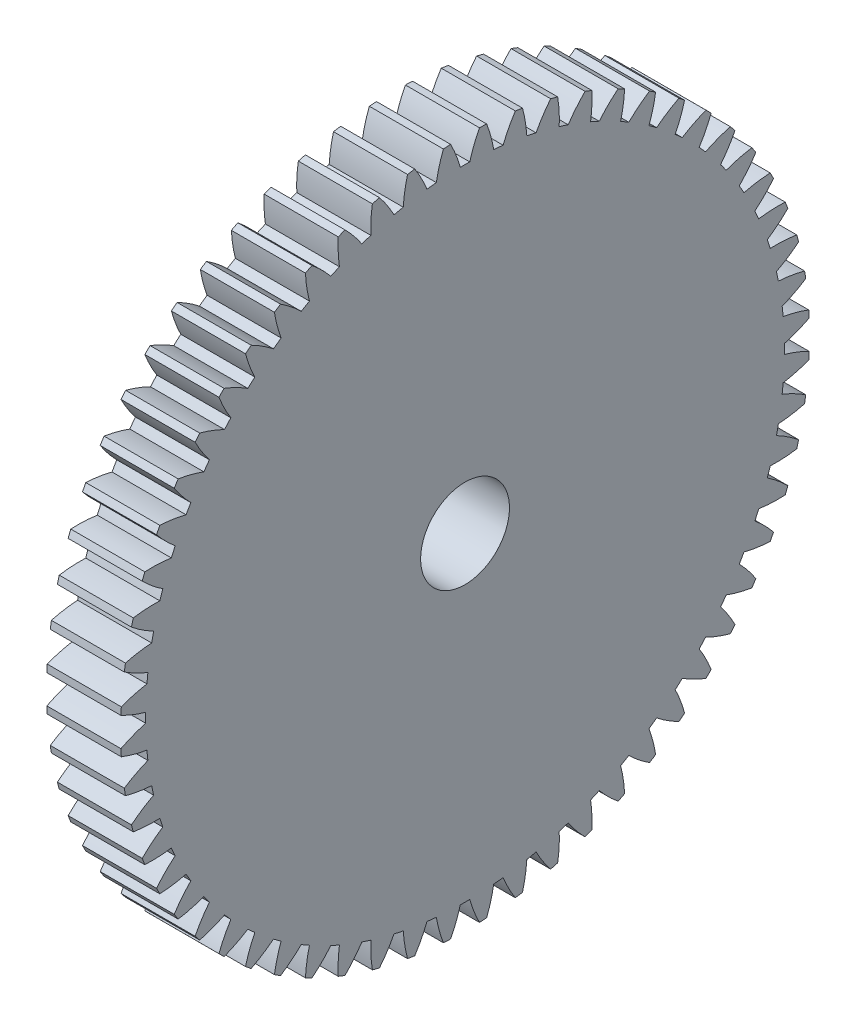
SolidWorks part; units mm, degrees
ref_plane "Plane1" through (0, 0, 0) normal (0, 0, 1) x (1, 0, 0)
ref_plane "Plane2" through (0, 0, 0) normal (0, 1, 0) x (1, 0, 0)
ref_plane "Plane3" through (0, 0, 0) normal (1, 0, 0) x (0, 0, -1)
other "Configuration Table"
sketch "HoldingSke" plane through (0, 0, 0) normal (0, 1, 0) x (1, 0, 0)
  line L0 (0, 0) -> (0.3333, -0.5774)
  line L1 (-15, 0) -> (100, 0) construction
  line L2 (0, 0) -> (-2.1039, 2.3779)
  line L3 (0, 0) -> (-11.863, 4.5341)
  line L4 (0, 0) -> (4.318, 7.479)
  line L5 (0, 0) -> (-46.8476, -17.4728)
  line L6 (0, 0) -> (-8.2896, -5.593)
  line L7 (-2.1039, 2.3779) -> (8.6586, 51.2059)
  line L8 (-76.2, 54.61) -> (-73.9, 54.61)
  line L9 (-71.009, 38.7566) -> (-53.1078, 45.2721)
  line L10 (-76.2, 71.12) -> (104.1128, 71.12)
  line L11 (0, 0) -> (-10, 0)
  line L12 (-76.2, 101.6) -> (-76.147, 101.6)
  line L13 (24.9733, 27.94) -> (52.9518, 28.4284)
  line L14 (24.9733, 27.94) -> (24.9743, 27.94)
  line L15 (24.9733, 27.94) -> (100.4006, 29.5858)
  line L16 (-63.627, -1.5) -> (-12.827, -1.5)
  circle A0 centre (0, 0) radius 6
  circle A1 centre (0, 0) radius 37.5
  circle A2 centre (0, 0) radius 37.5
  circle A3 centre (0, 0) radius 6
  dimension "MHD" = 75
  dimension "Hub_dia" = 75
  dimension "Bore" = 12
  dimension "MBD" = 12
  dimension "Num_teeth" = 60
  dimension "Pitch" = 0.6667
  dimension "Overall_len" = 50
  dimension "Show_teeth" = 60
  dimension "Thickness" = 10
  dimension "OAL" = 50.0001
  dimension "T_dim" = 2.3
  dimension "Ap" = 20
  dimension "H" = 19.05
  dimension "Pitch_radius" = 180.3128
  dimension "Width" = 10
  dimension "Backlash" = 0.053
  dimension "Addendum_fac" = 1
  dimension "Dedendum_fac" = 1.25
  dimension "Clearance_fac" = 0.25
  dimension "Dedendum_add" = 0.001
  dimension "Module" = 1.5
sketch "BasProSke" plane through (0, 0, 0) normal (0, 1, 0) x (1, 0, 0)
  line L0 (-10, 0) -> (60, 0) construction
  line L1 (0, 0) -> (0, 46.5)
  line L2 (0, 0) -> (10, 0)
  line L3 (10, 0) -> (10, 46.5)
  line L4 (10, 46.5) -> (0, 46.5)
  dimension "Thickness" = 10
  dimension "Diameter" = 93
revolve "Base-Revolve" add sketch "BasProSke" angle 360 about L0
sketch "TooCutSke" plane through (0, 0, 0) normal (1, 0, 0) x (0, 0, -1)
  line L1 (0, 0) -> (0, 107) construction
  line L2 (0, 0) -> (-1.2707, 44.9821) construction
  line L3 (0, 0) -> (-4.7089, 89.8505) construction
  line L4 (-1.2707, 44.9821) -> (-2.3544, 44.9253) construction
  arc A0 (0.6387, 43.1193) -> (-0.6387, 43.1193) centre (0, 0) ccw
  arc A1 (1.9554, 46.4843) -> (-1.9554, 46.4843) centre (0, 0) ccw
  circle A2 centre (0, 0) radius 45 construction
  circle A3 centre (0, 0) radius 42.2862 construction
  arc A4 (-0.6387, 43.1193) -> (-1.9554, 46.4843) centre (-17.9747, 38.2757) ccw
  arc A5 (1.9554, 46.4843) -> (0.6387, 43.1193) centre (17.9747, 38.2757) ccw
  dimension "Root_dia" = 86.248
  dimension "Overcut_dia" = 93.0508
  dimension "Pitch_dia" = 90
  dimension "Base_dia" = 84.5723
  dimension "Flank_rad" = 18
  dimension "Half_ang" = 3
  dimension "Half_CT" = 1.0852
extrude "ToothCut" cut sketch "TooCutSke" along normal through all
fillet "Breaks" [suppressed] radius 0.03
fillet "RootFillets" [suppressed] radius 0.376
pattern_circular "TeethCuts" count 60 every 6 about axis through (-10, 0, 0) along (1, 0, 0) of "ToothCut", "RootFillets", "Breaks"
sketch "HubNeaOneSke" plane through (0, 0, 0) normal (-1, 0, 0) x (0, 0, 1)
  circle A0 centre (0, 0) radius 37.5
  dimension "Diameter" = 75
extrude "HubNearOne" [suppressed] add sketch "HubNeaOneSke" along normal blind 40.0001
sketch "HubNeaBotSke" plane through (0, 0, 0) normal (-1, 0, 0) x (0, 0, 1)
  circle A0 centre (0, 0) radius 37.5
  dimension "Diameter" = 75
extrude "HubNearBoth" [suppressed] add sketch "HubNeaBotSke" along normal blind 20
ref_plane "FarPln" through (10, 0, 0) normal (1, 0, 0) x (0, 0, -1)
sketch "HubFarSke" plane through (10, 0, 0) normal (1, 0, 0) x (0, 0, -1)
  circle A0 centre (0, 0) radius 37.5
  dimension "Diameter" = 75
extrude "HubFar" [suppressed] add sketch "HubFarSke" along normal blind 20
sketch "BorSke" plane through (0, 0, 0) normal (1, 0, 0) x (0, 0, -1)
  circle A0 centre (0, 0) radius 6
  dimension "Diameter" = 12
extrude "Bore" cut sketch "BorSke" along normal mid plane 100.0001
sketch "KeySke" plane through (0, 0, 0) normal (1, 0, 0) x (0, 0, -1)
  line L0 (-2.5, 0) -> (-2.5, 8.3)
  line L1 (-2.5, 8.3) -> (2.5, 8.3)
  line L2 (2.5, 8.3) -> (2.5, 0)
  line L3 (0, 0) -> (0, 34) construction
  line L4 (-2.5, 0) -> (2.5, 0)
  dimension "Offset" = 8.3
  dimension "Width" = 5
extrude "Keyway" [suppressed] cut sketch "KeySke" along normal mid plane 100.0001
pattern_circular "Keyway2" [suppressed] count 2 every 90 about axis through (-10, 0, 0) along (1, 0, 0)
equation "' \"Module@HoldingSke\" = 6.35"
equation "' \"Num_teeth@HoldingSke\" = 12"
equation "' \"Ap@HoldingSke\" =  20"
equation "' \"Ap@HoldingSke\" = 20"
equation "' \"Width@HoldingSke\" = 0.5 * 25.4"
equation "' \"Hub_dia@HoldingSke\"= 1 * 25.4"
equation "' \"Hub_dia@HoldingSke\" = 1 * 25.4"
equation "' \"Overall_len@HoldingSke\" = 1.0 * 25.4"
equation "' \"Bore@HoldingSke\" = 0.75 * 25.4"
equation "' \"T_dim@HoldingSke\" = 0.1 * 25.4"
equation "' \"Width@KeySke\" = 0.25 * 25.4"
equation "' \"Show_teeth@HoldingSke\" = 13"
equation "' \"Backlash@HoldingSke\" = 0.009 * 25.4"
equation "' \"Addendum_fac@HoldingSke\" = 1.0"
equation "' \"Dedendum_fac@HoldingSke\" = 1.25"
equation "' \"Dedendum_add@HoldingSke\" = 0.00005 * 25.4"
equation "' \"Clearance_fac@HoldingSke\" = 0.25"
equation "\"Pitch@HoldingSke\" = 1 / \"Module@HoldingSke\""
equation "\"Overcut_dia@TooCutSke\" = (\"Num_teeth@HoldingSke\" + 2 * \"Addendum_fac@HoldingSke\") / \"Pitch@HoldingSke\" + 0.002 * 25.4"
equation "\"Pitch_dia@TooCutSke\" = \"Num_teeth@HoldingSke\" / \"Pitch@HoldingSke\""
equation "\"Base_dia@TooCutSke\" = \"Num_teeth@HoldingSke\" / \"Pitch@HoldingSke\" * cos((\"Ap@HoldingSke\"  * 3.14159265 / 180))"
equation "\"Root_dia@TooCutSke\" = (\"Num_teeth@HoldingSke\" + 2) / \"Pitch@HoldingSke\" - 2 * (\"Addendum_fac@HoldingSke\" + \"Dedendum_fac@HoldingSke\") / \"Pitch@HoldingSke\" - \"Dedendum_add@HoldingSke\" * 2"
equation "\"Half_ang@TooCutSke\" = 180 / \"Num_teeth@HoldingSke\""
equation "\"Half_CT@TooCutSke\" = \"Num_teeth@HoldingSke\" / \"Pitch@HoldingSke\" * sin((3.14159265 / 2 / \"Num_teeth@HoldingSke\")) / 2 - 7 * \"Backlash@HoldingSke\" / 4"
equation "\"Flank_rad@TooCutSke\" = \"Num_teeth@HoldingSke\" / \"Pitch@HoldingSke\" / 5"
equation "\"Radius@RootFillets\" = \"Clearance_fac@HoldingSke\" / \"Pitch@HoldingSke\" + \"Dedendum_add@HoldingSke\""
equation "\"Break_rad@Breaks\" = 0.02 / \"Pitch@HoldingSke\""
equation "\"Thickness@HoldingSke\" = \"Width@HoldingSke\""
equation "\"OAL@HoldingSke\" = \"Thickness@HoldingSke\""
equation "\"MHD@HoldingSke\" = (\"Num_teeth@HoldingSke\" + 2) / \"Pitch@HoldingSke\" - 2 * (\"Addendum_fac@HoldingSke\" + \"Dedendum_fac@HoldingSke\")  / \"Pitch@HoldingSke\" - \"Dedendum_add@HoldingSke\" * 2"
equation "\"MBD@HoldingSke\" = (\"Num_teeth@HoldingSke\" + 2) / \"Pitch@HoldingSke\" - 2 * (\"Addendum_fac@HoldingSke\" + \"Dedendum_fac@HoldingSke\")  / \"Pitch@HoldingSke\" - \"Dedendum_add@HoldingSke\" * 2 - 0.002 * 25.4"
equation "\"MHD@HoldingSke\" = ((sgn( \"MHD@HoldingSke\" - \"Hub_dia@HoldingSke\" )-1)*( \"MHD@HoldingSke\" - \"Hub_dia@HoldingSke\" ))/-2+ \"Hub_dia@HoldingSke\""
equation "\"MBD@HoldingSke\" = ((sgn( \"MBD@HoldingSke\" - \"Bore@HoldingSke\" )-1)*( \"MBD@HoldingSke\" - \"Bore@HoldingSke\" ))/-2+ \"Bore@HoldingSke\""
equation "\"OAL@HoldingSke\" = ((sgn( \"OAL@HoldingSke\" - \"Overall_len@HoldingSke\" )+1)*( \"OAL@HoldingSke\" - \"Overall_len@HoldingSke\" ))/2 + \"Overall_len@HoldingSke\" + 0.000002 * 25.4"
equation "\"Num_teeth@TeethCuts\" = int( \"Show_teeth@HoldingSke\" ) + 1"
equation "\"Num_teeth@TeethCuts\" = ((sgn( \"Num_teeth@TeethCuts\" - \"Num_teeth@HoldingSke\" )-1)*( \"Num_teeth@TeethCuts\" - \"Num_teeth@HoldingSke\" ))/-2+ \"Num_teeth@HoldingSke\""
equation "\"Num_teeth@TeethCuts\" = ((sgn( \"Num_teeth@TeethCuts\" - 2.0)+1)*( \"Num_teeth@TeethCuts\" - 2.0))/2 +2.0"
equation "\"Angle@TeethCuts\" = 360.0 / \"Num_teeth@HoldingSke\""
equation "\"Diameter@BasProSke\" = (\"Num_teeth@HoldingSke\" + 2 * \"Addendum_fac@HoldingSke\") / \"Pitch@HoldingSke\""
equation "\"Thickness@BasProSke\"  = \"Thickness@HoldingSke\""
equation "' \"Fillet_rad@BasProSke\" =  \"Thickness@HoldingSke\" * 0.05"
equation "' \"Fillet_rad@BasProSke\" = \"Thickness@HoldingSke\" * 0.05"
equation "\"MHD@HoldingSke\" = ((sgn( \"MHD@HoldingSke\" - \"Root_dia@TooCutSke\" )-1)*( \"MHD@HoldingSke\" - \"Root_dia@TooCutSke\" ))/-2+ \"Root_dia@TooCutSke\""
equation "\"Diameter@HubNeaOneSke\" = \"MHD@HoldingSke\""
equation "\"Length@HubNearOne\" = \"OAL@HoldingSke\" - \"Thickness@BasProSke\""
equation "\"Diameter@HubNeaBotSke\" = \"MHD@HoldingSke\""
equation "\"Length@HubNearBoth\" = ( \"OAL@HoldingSke\" - \"Thickness@BasProSke\" ) / 2.0"
equation "\"Thickness@FarPln\" = \"Thickness@BasProSke\""
equation "\"Diameter@HubFarSke\" = \"MHD@HoldingSke\""
equation "\"Length@HubFar\" = ( \"OAL@HoldingSke\" - \"Thickness@BasProSke\" ) / 2.0"
equation "\"Diameter@BorSke\" = \"MBD@HoldingSke\""
equation "\"D1@Bore\" = \"OAL@HoldingSke\" * 2.0"
equation "\"D1@Keyway\" = \"OAL@HoldingSke\" * 2.0"
equation "\"Offset@KeySke\" = \"T_dim@HoldingSke\" + \"MBD@HoldingSke\" / 2.0"
